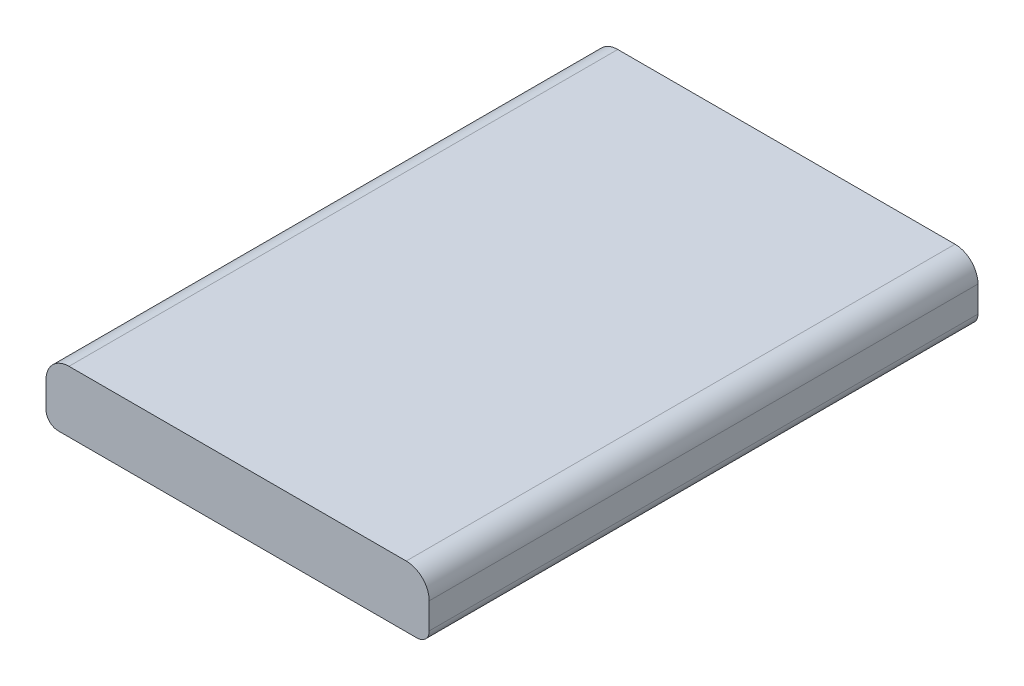
SolidWorks part; units mm, degrees
ref_plane "Front Plane" through (0, 0, 0) normal (0, 0, 1) x (1, 0, 0)
ref_plane "Top Plane" through (0, 0, 0) normal (0, 1, 0) x (1, 0, 0)
ref_plane "Right Plane" through (0, 0, 0) normal (1, 0, 0) x (0, 0, -1)
sketch "Sketch1" plane through (0, 0, 0) normal (0, 1, 0) x (1, 0, 0)
  line L1 (-12.5, 17.9) -> (12.5, 17.9)
  line L2 (-12.5, 17.9) -> (-12.5, -17.9)
  line L3 (-12.5, -17.9) -> (12.5, -17.9)
  line L4 (12.5, 17.9) -> (12.5, -17.9)
  line L5 (-12.5, 17.9) -> (12.5, -17.9) construction
  line L6 (-12.5, -17.9) -> (12.5, 17.9) construction
  point P0 (0, 0)
  dimension "D1" = 25
  dimension "D2" = 35.8
extrude "Boss-Extrude1" add sketch "Sketch1" along normal blind 4
fillet "Fillet1" radius 1.5 2 edges at (-12.5, 4, 0) (12.5, 4, 0)
fillet "Fillet2" radius 0.8 2 edges at (-12.5, 0, 0) (12.5, 0, 0)
